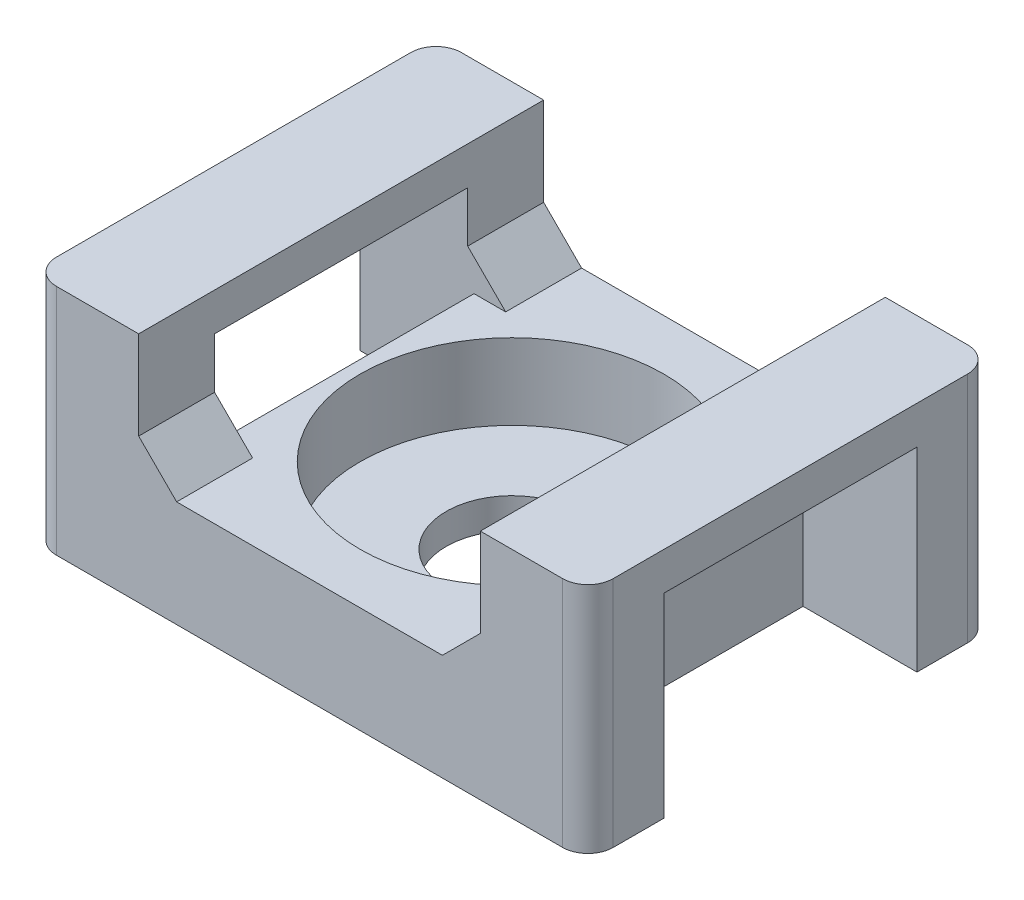
SolidWorks part; units mm, degrees
material "Пластик"
ref_plane "Спереди" through (0, 0, 0) normal (0, 0, 1) x (1, 0, 0)
ref_plane "Сверху" through (0, 0, 0) normal (0, 1, 0) x (1, 0, 0)
ref_plane "Справа" through (0, 0, 0) normal (1, 0, 0) x (0, 0, -1)
sketch "Эскиз1" plane through (0, 0, 0) normal (0, 0, 1) x (1, 0, 0)
  line L7 (11, 0) -> (-11, 0)
  line L8 (-11, 0) -> (-11, 9.2)
  line L9 (-11, 9.2) -> (-6.75, 9.2)
  line L10 (-6.75, 9.2) -> (-6.75, 5.7)
  line L11 (-6.75, 5.7) -> (-5.25, 4.2)
  line L12 (-5.25, 4.2) -> (5.25, 4.2)
  line L13 (0, 4.2) -> (0, 0) construction
  line L14 (6.75, 5.7) -> (5.25, 4.2)
  line L15 (6.75, 9.2) -> (6.75, 5.7)
  line L16 (11, 9.2) -> (6.75, 9.2)
  line L17 (11, 0) -> (11, 9.2)
  point P14 (-5.1092, 4.2)
  dimension "D1" = 22
  dimension "D2" = 13.5
  dimension "D3" = 9.2
  dimension "D4" = 4.2
  dimension "D5" = 135
  dimension "D6" = 1.5
extrude "Бобышка-Вытянуть1" add sketch "Эскиз1" along normal mid plane 16
sketch "Эскиз2" plane through (0, 0, 0) normal (0, 0, 1) x (1, 0, 0)
  line L0 (-11, 7.7) -> (-6.75, 7.7)
  line L1 (-11, 9.2) -> (-11, 0) construction
  line L2 (-6.75, 5.7) -> (-6.75, 9.2) construction
  line L3 (-6.75, 7.7) -> (-6.75, 5.7)
  line L4 (-6.75, 5.7) -> (-5.25, 4.2)
  line L5 (-5.25, 4.2) -> (-6.5, 4.2)
  line L6 (-6.5, 4.2) -> (-6.5, 0)
  line L7 (-11, 0) -> (11, 0) construction
  line L8 (-6.5, 0) -> (-11, 0)
  line L9 (-11, 0) -> (-11, 7.7)
  line L10 (0, 0) -> (0, 4.2) construction
  line L11 (5.25, 4.2) -> (-5.25, 4.2) construction
  dimension "D1" = 7.7
  dimension "D2" = 13
extrude "Вырез-Вытянуть1" cut sketch "Эскиз2" against normal mid plane 10
mirror "Зеркальное отражение1" about plane through (0, 0, 0) normal (1, 0, 0) of "Вырез-Вытянуть1"
hole_wizard "Цековка для  болта с шестигранной головкой M51" positions "Эскиз3" profile "Эскиз5" counterbore size "M5" standard "ISO" end condition up to next
sketch "Эскиз3" plane through (0, 4.2, 0) normal (0, 1, 0) x (1, 0, 0)
  point P0 (0, 0)
sketch "Эскиз5" plane through (0, 4.2, 0) normal (1, 0, 0) x (0, 0, 1)
  line L0 (0, 0) -> (0, 4.2)
  line L1 (0, 4.2) -> (2.6, 4.2)
  line L3 (2.6, 4.2) -> (2.6, 3)
  line L4 (2.6, 3) -> (6, 3)
  line L5 (6, 3) -> (6, 0)
  line L7 (6, 0) -> (0, 0)
  line L11 (0, -6.35) -> (0, 107.95) construction
  dimension "Диаметр сквозного отверстия" = 5.2
  dimension "Глубина сквозного отверстия" = 4.2
  dimension "Диаметр цековки" = 12
  dimension "Глубина цековки" = 3
fillet "Скругление1" radius 1 4 edges at (11, 4.6, -8) (-11, 4.6, -8) (11, 4.6, 8) (-11, 4.6, 8)
